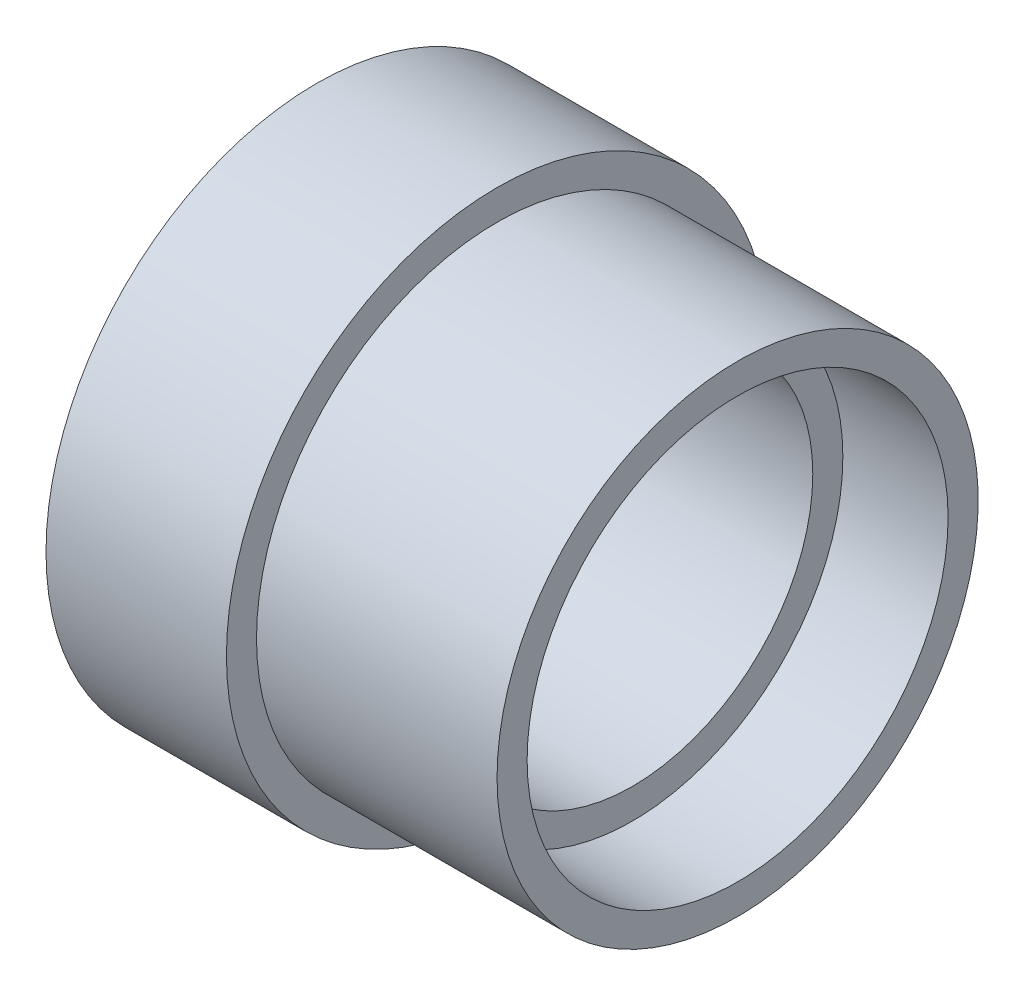
SolidWorks part; units mm, degrees
material "AISI 1020"
ref_plane "Спереди" through (0, 0, 0) normal (0, 0, 1) x (1, 0, 0)
ref_plane "Сверху" through (0, 0, 0) normal (0, 1, 0) x (1, 0, 0)
ref_plane "Справа" through (0, 0, 0) normal (1, 0, 0) x (0, 0, -1)
sketch "Эскиз1" plane through (0, 0, 0) normal (0, 0, 1) x (1, 0, 0)
  line L0 (-3, -142) -> (-3, -140)
  line L1 (-3, -140) -> (-19, -140)
  line L2 (-19, -140) -> (-19, -138)
  line L3 (-19, -120) -> (-19, -142.2631) construction
  line L4 (-19, -138) -> (-31, -138)
  line L5 (-31, -138) -> (-31, -142)
  line L6 (-31, -142) -> (-24, -142)
  line L7 (-24, -142) -> (-24, -144)
  line L8 (-24, -144) -> (-10, -144)
  line L10 (-10, -144) -> (-10, -142)
  line L12 (-10, -142) -> (-3, -142)
  line L13 (-15, -140) -> (-19, -140) construction
  line L14 (-1017, -156) -> (48983, -156) construction
  line L15 (-31, -142) -> (-31, -170) construction
  line L16 (-31, -142) -> (-31, -170) construction
  line L17 (-3, -142) -> (-3, -170) construction
  line L18 (-3, -142) -> (-3, -170) construction
  line L19 (-24, -169) -> (-24, -143) construction
  line L20 (-24, -169) -> (-24, -143) construction
  line L21 (-10, -143) -> (-10, -169) construction
  line L22 (-10, -143) -> (-10, -169) construction
  dimension "D1" = 2
  dimension "D2" = 2
revolve "Повернуть1" add sketch "Эскиз1" angle 360 about L14
